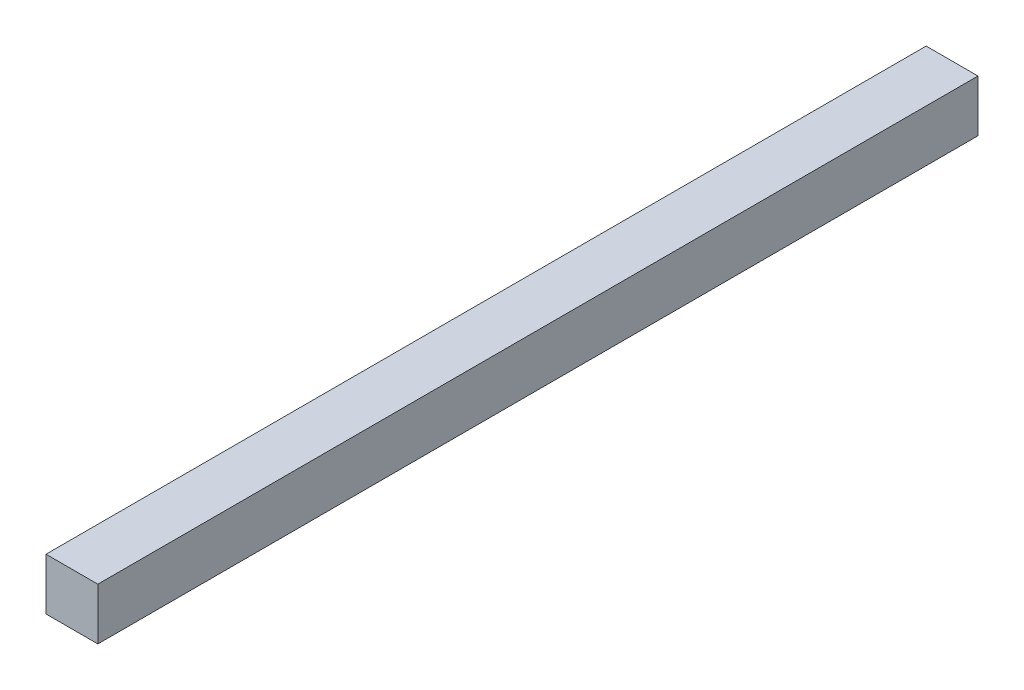
SolidWorks part; units mm, degrees
ref_plane "Plano frontal" through (0, 0, 0) normal (0, 0, 1) x (1, 0, 0)
ref_plane "Plano superior" through (0, 0, 0) normal (0, 1, 0) x (1, 0, 0)
ref_plane "Plano direito" through (0, 0, 0) normal (1, 0, 0) x (0, 0, -1)
sketch "Esboço2" plane through (0, 0, 0) normal (0, 0, 1) x (1, 0, 0)
  line L1 (-110.6583, 30) -> (-80.6129, 30)
  line L2 (-110.6583, 30) -> (-110.6583, 0)
  line L3 (-110.6583, 0) -> (-80.6129, 0)
  line L4 (-80.6129, 30) -> (-80.6129, 0)
  dimension "D1" = 30
  dimension "D2" = 30.0454
extrude "Ressalto-extrusão1" add sketch "Esboço2" along normal mid plane 510
